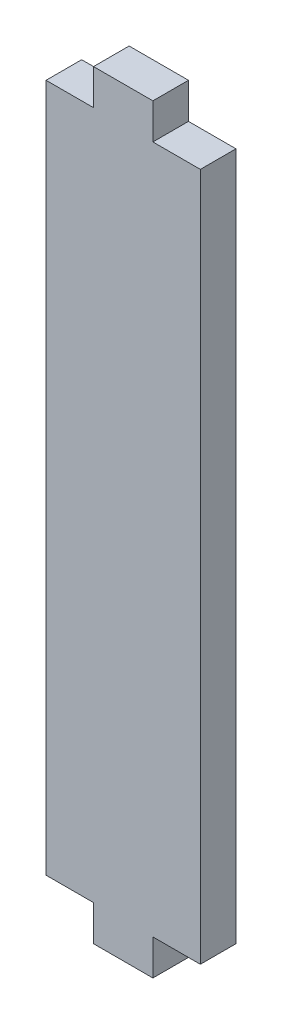
SolidWorks part; units mm, degrees
ref_plane "Alzado" through (0, 0, 0) normal (0, 0, 1) x (1, 0, 0)
ref_plane "Planta" through (0, 0, 0) normal (0, 1, 0) x (1, 0, 0)
ref_plane "Vista lateral" through (0, 0, 0) normal (1, 0, 0) x (0, 0, -1)
sketch "Croquis1" plane through (0, 0, 0) normal (0, 0, 1) x (1, 0, 0)
  line L0 (-6.5, 29) -> (-2.5, 29)
  line L2 (-6.5, 29) -> (-6.5, -29)
  line L4 (6.5, 29) -> (6.5, -29)
  line L5 (-6.5, 29) -> (6.5, -29) construction
  line L6 (-6.5, -29) -> (6.5, 29) construction
  line L7 (-2.5, 29) -> (-2.5, 32)
  line L8 (-2.5, 32) -> (2.5, 32)
  line L9 (2.5, 32) -> (2.5, 29)
  line L10 (2.5, 29) -> (6.5, 29)
  line L11 (6.5, -29) -> (2.5, -29)
  line L12 (2.5, -29) -> (2.5, -32)
  line L13 (2.5, -32) -> (-2.5, -32)
  line L14 (-2.5, -32) -> (-2.5, -29)
  line L15 (-2.5, -29) -> (-6.5, -29)
  point P0 (0, 0)
  dimension "D1" = 5
  dimension "D2" = 3
  dimension "D3" = 13
  dimension "D4" = 58
extrude "Saliente-Extruir1" add sketch "Croquis1" along normal blind 3
